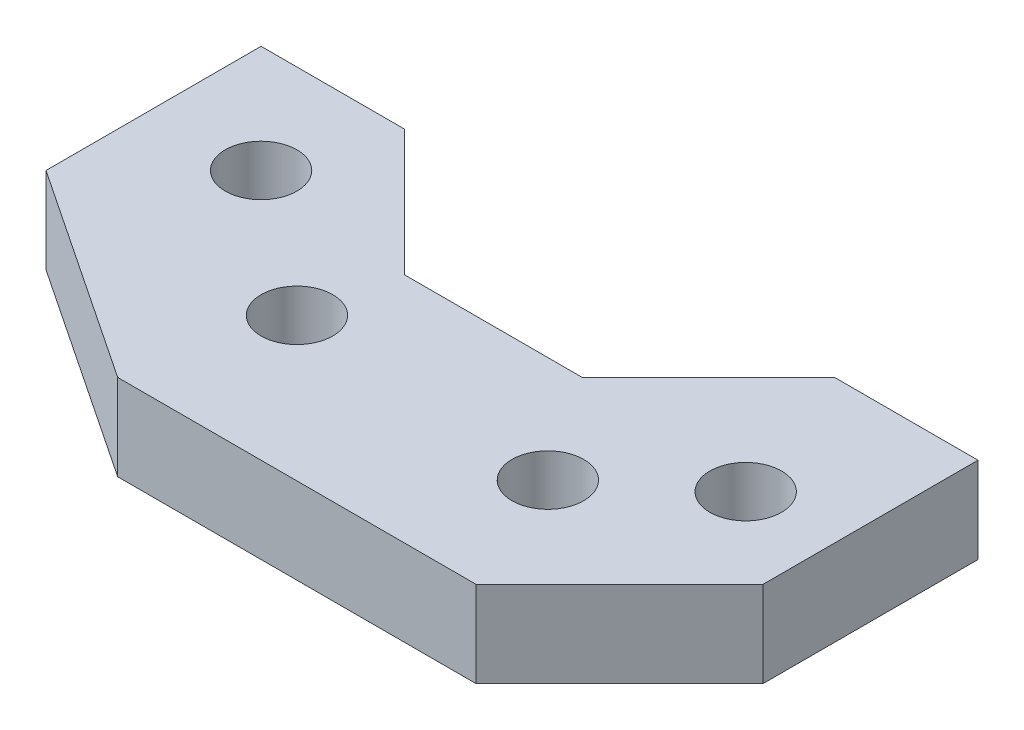
SolidWorks part; units mm, degrees
ref_plane "Front Plane" through (0, 0, 0) normal (0, 0, 1) x (1, 0, 0)
ref_plane "Top Plane" through (0, 0, 0) normal (0, 1, 0) x (1, 0, 0)
ref_plane "Right Plane" through (0, 0, 0) normal (1, 0, 0) x (0, 0, -1)
sketch "Sketch1" plane through (0, 0, 0) normal (0, 1, 0) x (1, 0, 0)
  line L4 (79.248, -22.352) -> (101.6, 0)
  line L5 (127, 0) -> (101.6, 0)
  line L6 (38.1, -63.5) -> (101.6, -63.5)
  line L7 (0, -38.1) -> (38.1, -63.5)
  line L8 (0, 0) -> (0, -38.1)
  line L9 (0, 0) -> (25.4, 0)
  line L10 (25.4, 0) -> (47.752, -22.352)
  line L11 (47.752, -22.352) -> (79.248, -22.352)
  line L13 (101.6, -63.5) -> (127, -38.1)
  line L14 (127, 0) -> (127, -38.1)
  circle A0 centre (19.05, -19.05) radius 6.35
  circle A1 centre (111.252, -25.4) radius 6.35
  circle A2 centre (44.45, -38.1) radius 6.35
  circle A3 centre (91.948, -41.148) radius 6.35
  dimension "D5" = 47.752
  dimension "D7" = 15.748
  dimension "D17" = 12.7
  dimension "D18" = 12.7
  dimension "D19" = 12.7
  dimension "D20" = 22.352
  dimension "D22" = 12.7
  dimension "D1" = 127
  dimension "D2" = 25.4
  dimension "D3" = 25.4
  dimension "D4" = 47.752
  dimension "D6" = 19.05
  dimension "D8" = 22.352
  dimension "D9" = 63.5
  dimension "D10" = 38.1
  dimension "D11" = 25.4
  dimension "D12" = 38.1
  dimension "D13" = 25.4
  dimension "D14" = 45
  dimension "D15" = 63.5
  dimension "D16" = 44.45
  dimension "D21" = 47.498
  dimension "D23" = 25.4
  dimension "D24" = 19.05
extrude "Boss-Extrude1" add sketch "Sketch1" along normal blind 15.24
